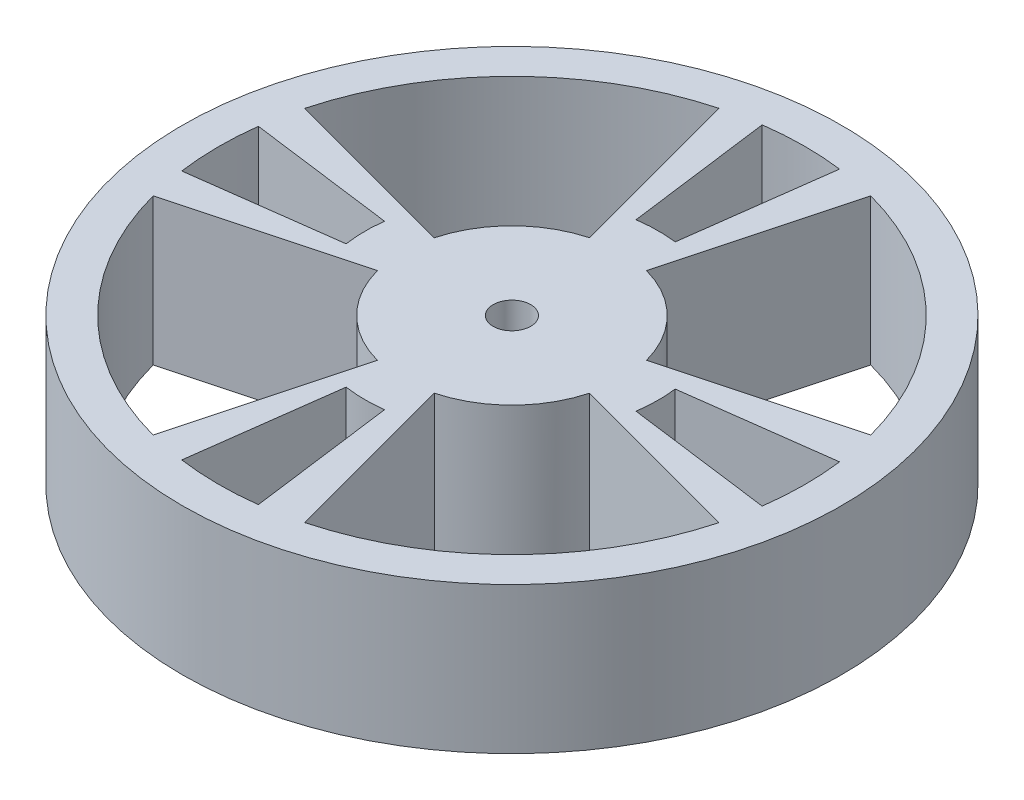
SolidWorks part; units mm, degrees
ref_plane "Front Plane" through (0, 0, 0) normal (0, 0, 1) x (1, 0, 0)
ref_plane "Top Plane" through (0, 0, 0) normal (0, 1, 0) x (1, 0, 0)
ref_plane "Right Plane" through (0, 0, 0) normal (1, 0, 0) x (0, 0, -1)
sketch "Sketch1" plane through (0, 0, 0) normal (0, 1, 0) x (1, 0, 0)
  circle A0 centre (0, 0) radius 9.525
  dimension "D1" = 19.05
extrude "Boss-Extrude1" add sketch "Sketch1" along normal blind 2.54
sketch "Sketch3" plane through (0, 2.54, 0) normal (0, 1, 0) x (1, 0, 0)
  line L0 (0, 0) -> (28.575, 0) construction
  line L1 (0, 0) -> (0, 28.575) construction
  line L2 (0, 0) -> (27.6013, 7.3958) construction
  line L3 (-2.4653, 9.2004) -> (-6.574, 24.5345)
  line L4 (9.2004, 2.4653) -> (24.5345, 6.574)
  line L5 (-9.2004, 2.4653) -> (-24.5345, 6.574)
  line L6 (0, 0) -> (20.2056, 20.2056) construction
  line L8 (2.4653, 9.2004) -> (6.574, 24.5345)
  line L9 (9.2004, -2.4653) -> (24.5345, -6.574)
  line L10 (2.4653, -9.2004) -> (6.574, -24.5345)
  line L11 (-9.2004, -2.4653) -> (-24.5345, -6.574)
  line L12 (-2.4653, -9.2004) -> (-6.574, -24.5345)
  circle A0 centre (0, 0) radius 28.575
  circle A2 centre (0, 0) radius 25.4 construction
  circle A3 centre (0, 0) radius 9.525 construction
  arc A4 (-9.2004, 2.4653) -> (-2.4653, 9.2004) centre (0, 0) cw
  arc A5 (9.2004, 2.4653) -> (2.4653, 9.2004) centre (0, 0) ccw
  arc A8 (24.5345, 6.574) -> (6.574, 24.5345) centre (0, 0) ccw
  arc A9 (-24.5345, 6.574) -> (-6.574, 24.5345) centre (0, 0) cw
  arc A10 (9.2004, -2.4653) -> (2.4653, -9.2004) centre (0, 0) cw
  arc A11 (24.5345, -6.574) -> (6.574, -24.5345) centre (0, 0) cw
  arc A12 (-24.5345, -6.574) -> (-6.574, -24.5345) centre (0, 0) ccw
  arc A13 (-9.2004, -2.4653) -> (-2.4653, -9.2004) centre (0, 0) ccw
  dimension "D1" = 57.15
  dimension "D2" = 15
  dimension "D4" = 3.175
  dimension "D3" = 45
extrude "Boss-Extrude2" add sketch "Sketch3" along normal blind 12.7
sketch "Sketch4" plane through (0, 15.24, 0) normal (0, 1, 0) x (1, 0, 0)
  line L0 (0, 0) -> (28.575, 0) construction
  line L1 (0, 0) -> (0, 28.575) construction
  line L2 (12.6046, 1.5541) -> (25.1961, 3.2118)
  line L5 (12.5705, -1.8088) -> (25.1623, -3.4665)
  line L6 (-12.6046, 1.5541) -> (-25.1961, 3.2118)
  line L7 (-12.5705, -1.8088) -> (-25.1623, -3.4665)
  line L8 (0, 0) -> (20.2056, 20.2056) construction
  line L9 (1.5541, 12.6046) -> (3.2118, 25.1961)
  line L10 (-1.8088, 12.5705) -> (-3.4665, 25.1623)
  line L11 (-1.8088, -12.5705) -> (-3.4665, -25.1623)
  line L12 (1.5541, -12.6046) -> (3.2118, -25.1961)
  circle A2 centre (0, 0) radius 12.7 construction
  arc A3 (-2.4653, 9.2004) -> (-9.2004, 2.4653) centre (0, 0) ccw construction
  circle A4 centre (0, 0) radius 25.4 construction
  arc A5 (12.5705, -1.8088) -> (12.6046, 1.5541) centre (0, 0) ccw
  arc A6 (-6.574, 24.5345) -> (-24.5345, 6.574) centre (0, 0) ccw construction
  circle A7 centre (0, 0) radius 28.575 construction
  arc A8 (25.1623, -3.4665) -> (25.1961, 3.2118) centre (0, 0) ccw
  arc A9 (-12.5705, -1.8088) -> (-12.6046, 1.5541) centre (0, 0) cw
  arc A10 (-25.1623, -3.4665) -> (-25.1961, 3.2118) centre (0, 0) cw
  arc A11 (-1.8088, 12.5705) -> (1.5541, 12.6046) centre (0, 0) cw
  arc A12 (-3.4665, 25.1623) -> (3.2118, 25.1961) centre (0, 0) cw
  arc A13 (-3.4665, -25.1623) -> (3.2118, -25.1961) centre (0, 0) ccw
  arc A14 (-1.8088, -12.5705) -> (1.5541, -12.6046) centre (0, 0) ccw
  dimension "D1" = 3.175
  dimension "D2" = 0
  dimension "D3" = 7.5
  dimension "D4" = 7.5
  dimension "D5" = 45
extrude "Cut-Extrude2" cut sketch "Sketch4" against normal through all
sketch "Sketch2" plane through (0, 0, 0) normal (0, 1, 0) x (1, 0, 0)
  line L1 (-4.5529, 1.8859) -> (-1.8859, 4.5529)
  line L2 (-2.667, 2.667) -> (2.667, -2.667) construction
  line L3 (0, 2.667) -> (-1.8859, 4.5529)
  line L4 (1.8859, 4.5529) -> (4.5529, 1.8859)
  line L5 (0, 2.667) -> (1.8859, 4.5529)
  line L6 (0, -2.667) -> (1.8859, -4.5529)
  line L7 (-4.5529, -1.8859) -> (-1.8859, -4.5529)
  line L8 (-2.667, 0) -> (-4.5529, 1.8859)
  line L9 (1.8859, -4.5529) -> (4.5529, -1.8859)
  line L10 (-2.667, -2.667) -> (2.667, -2.667) construction
  line L11 (-2.667, 0) -> (-4.5529, -1.8859)
  line L12 (2.667, 0) -> (4.5529, 1.8859)
  line L13 (-2.667, 2.667) -> (2.667, 2.667) construction
  line L14 (2.667, 0) -> (4.5529, -1.8859)
  line L15 (2.667, -2.667) -> (2.667, 2.667) construction
  line L16 (-2.667, -2.667) -> (-2.667, 2.667) construction
  line L17 (0, -2.667) -> (-1.8859, -4.5529)
  line L18 (-2.667, -2.667) -> (2.667, 2.667) construction
  point P23 (-2.667, 0)
  dimension "D1" = 3.7717
  dimension "D2" = 2.667
  dimension "D3" = 2.667
  dimension "D4" = 3.7717
  dimension "D5" = 2.667
  dimension "D6" = 2.667
  dimension "D7" = 3.7717
  dimension "D8" = 2.667
  dimension "D9" = 2.667
  dimension "D10" = 3.7717
  dimension "D11" = 2.667
  dimension "D12" = 2.667
  dimension "D13" = 5.334
  dimension "D14" = 5.334
  dimension "D15" = 3.7717
extrude "Cut-Extrude3" cut sketch "Sketch2" along normal blind 8.4667
sketch "Sketch5" plane through (0, 15.24, 0) normal (0, 1, 0) x (1, 0, 0)
  circle A0 centre (0, 0) radius 1.632
  dimension "D1" = 3.2639
extrude "Cut-Extrude4" cut sketch "Sketch5" against normal through all
